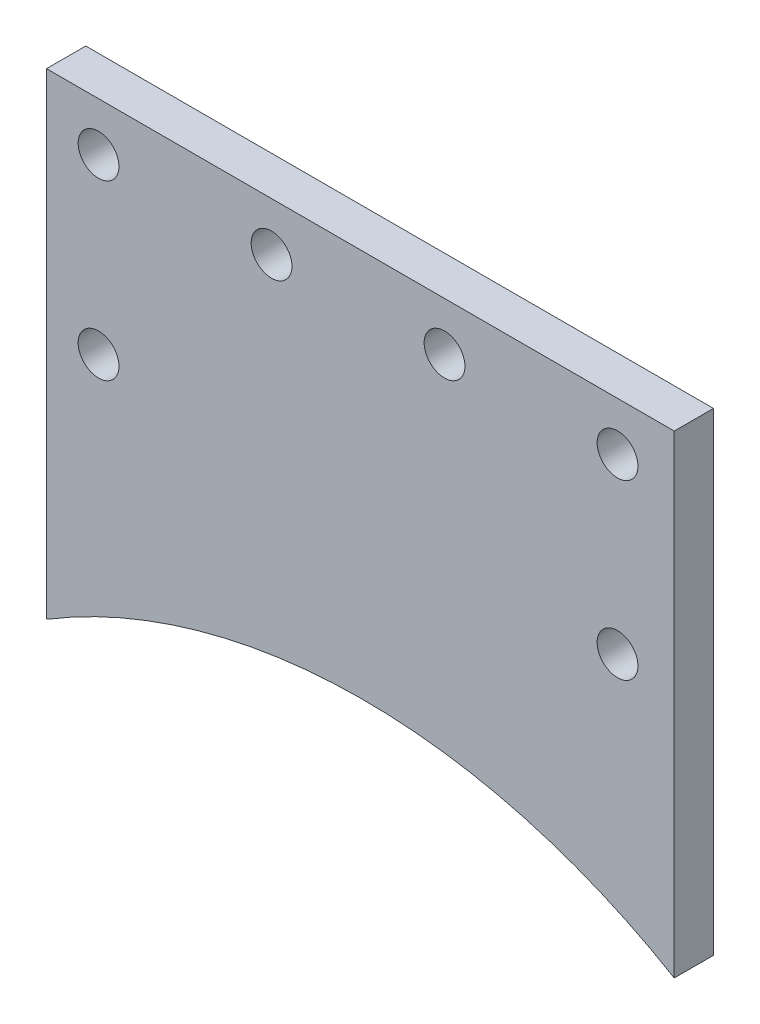
SolidWorks part; units mm, degrees
ref_plane "Front" through (0, 0, 0) normal (0, 0, 1) x (1, 0, 0)
ref_plane "Top" through (0, 0, 0) normal (0, 1, 0) x (1, 0, 0)
ref_plane "Right" through (0, 0, 0) normal (1, 0, 0) x (0, 0, -1)
sketch "Sketch1" plane through (0, 0, 0) normal (0, 0, 1) x (1, 0, 0)
  line L1 (-49.7376, 7.8601) -> (51.8624, 7.8601)
  line L2 (-49.7376, 7.8601) -> (-49.7376, -69.2499)
  line L3 (-49.7376, -69.2499) -> (51.8624, -69.2499)
  line L4 (51.8624, 7.8601) -> (51.8624, -69.2499)
  dimension "D1" = 101.6
  dimension "D2" = 77.11
extrude "Boss-Extrude1" add sketch "Sketch1" along normal blind 6.35
sketch "Sketch2" plane through (0, 0, 6.35) normal (0, 0, 1) x (1, 0, 0)
  circle A0 centre (1.5011, -153.5159) radius 98.5502
extrude "Cut-Extrude1" cut sketch "Sketch2" against normal through all
sketch "Sketch3" plane through (0, 0, 6.35) normal (0, 0, 1) x (1, 0, 0)
  line L0 (-41.3181, 0) -> (-13.3181, 0) construction
  circle A0 centre (-41.3181, 0) radius 3.302
  circle A1 centre (-13.3181, 0) radius 3.302
  circle A2 centre (14.6819, 0) radius 3.302
  circle A3 centre (42.6819, 0) radius 3.302
  circle A4 centre (-41.3181, -28) radius 3.302
  circle A5 centre (42.6819, -28) radius 3.302
  dimension "D1" = 28
  dimension "D3" = 6.604
  dimension "D2" = 4
extrude "Cut-Extrude2" cut sketch "Sketch3" against normal through all
